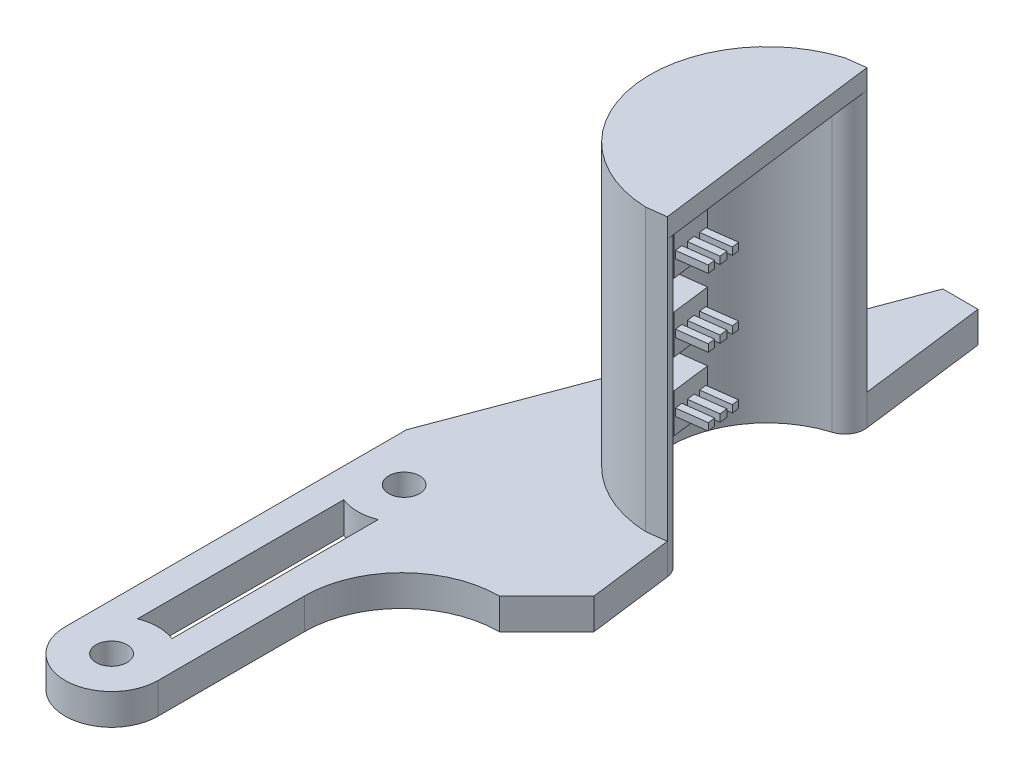
SolidWorks part; units mm, degrees
material "1060-H14"
ref_plane "Alzado" through (0, 0, 0) normal (0, 0, 1) x (1, 0, 0)
ref_plane "Planta" through (0, 0, 0) normal (0, 1, 0) x (1, 0, 0)
ref_plane "Vista lateral" through (0, 0, 0) normal (1, 0, 0) x (0, 0, -1)
sketch "Croquis1" plane through (0, 0, 0) normal (0, 1, 0) x (1, 0, 0)
  line L0 (-12.5, 40) -> (12.5, -40) construction
  line L1 (-12.5, 40) -> (12.5, 40) construction
  line L2 (-12.5, 40) -> (-12.5, -40) construction
  line L3 (-12.5, -40) -> (12.5, -40) construction
  line L4 (12.5, 40) -> (12.5, -40) construction
  line L5 (-12.5, 0) -> (-12.5, -40)
  line L6 (-12.5, -40) -> (-2.975, -40)
  line L7 (-2.975, -40) -> (-2.975, -20)
  line L8 (7.025, -10) -> (12.5, -10)
  line L9 (12.5, -10) -> (12.5, 40)
  line L10 (12.5, 40) -> (2.5, 40)
  line L11 (2.5, 40) -> (-12.5, 0)
  circle A0 centre (-7.7375, -5) radius 1.5875
  circle A1 centre (-7.7375, -35) radius 1.5875
  arc A2 (-2.975, -20) -> (7.025, -10) centre (7.025, -20) cw
  dimension "D5" = 3.175
  dimension "D6" = 3.175
  dimension "D12" = 10
  dimension "D1" = 25
  dimension "D2" = 80
  dimension "D3" = 9.525
  dimension "D4" = 30
  dimension "D7" = 4.7625
  dimension "D8" = 5
  dimension "D9" = 10
  dimension "D10" = 40
  dimension "D11" = 50
extrude "Saliente-Extruir1" add sketch "Croquis1" along normal blind 3.175
sketch "Croquis2" plane through (0, 3.175, 0) normal (0, 1, 0) x (1, 0, 0)
  line L0 (12.5, -10) -> (6.1, 40)
  line L1 (12.5, 40) -> (2.5, 40) construction
  line L2 (6.1, 40) -> (12.5, 40)
  line L3 (12.5, 40) -> (12.5, -10)
  dimension "D1" = 6.4
extrude "Cortar-Extruir1" cut sketch "Croquis2" against normal blind 3.175
sketch "Croquis3" plane through (0, 3.175, 0) normal (0, 1, 0) x (1, 0, 0)
  line L1 (-2.975, -40) -> (-2.975, -20) construction
  line L2 (-12.5, -35) -> (-12.5, -40)
  line L3 (-12.5, -40) -> (-2.975, -40)
  line L4 (-2.975, -40) -> (-2.975, -35)
  line L5 (-9.5, -9.4271) -> (-9.5, -30.5756)
  line L6 (-5.975, -14.8038) -> (-5.975, -30.5756)
  line L7 (-12.5, 0) -> (-12.5, -40) construction
  line L8 (-5.975, -14.8038) -> (-5.975, -9.4271)
  line L22 (7.025, -6) -> (7.9554, -6)
  line L23 (7.9554, -6) -> (3.2646, 30.6468)
  line L24 (3.2646, 30.6468) -> (-8.5, -0.7253)
  line L25 (-8.5, -0.7253) -> (-8.5, -36)
  line L26 (-8.5, -36) -> (-6.975, -36)
  line L27 (-6.975, -36) -> (-6.975, -20)
  line L28 (7.025, -6) -> (7.9554, -6)
  arc A2 (-9.5, -9.4271) -> (-5.975, -9.4271) centre (-7.7375, -5) ccw
  arc A3 (-12.5, -35) -> (-2.975, -35) centre (-7.7375, -35) ccw
  arc A4 (-5.975, -30.5756) -> (-9.5, -30.5756) centre (-7.7375, -35) ccw
  arc A6 (7.025, -6) -> (-6.975, -20) centre (7.025, -20) ccw
  dimension "D1" = 9.53
  dimension "D2" = 3
  dimension "D3" = 3
  dimension "D5" = 4
extrude "Cortar-Extruir3" cut sketch "Croquis3" against normal blind 10 contours A4 L6 L8 A2 L5 | A3 L4 L3 L2
sketch "Croquis4" plane through (0, 3.175, 0) normal (0, 1, 0) x (1, 0, 0)
  line L0 (6.1, 40) -> (12.5, -10) construction
  line L1 (7.025, -10) -> (11.8787, -5.1463)
  line L2 (11.8787, -5.1463) -> (12.5, -10)
  line L3 (12.5, -10) -> (7.025, -10)
  circle A0 centre (9.2741, 15.2023) radius 10
  dimension "D1" = 20
  dimension "D2" = 25
  dimension "D3" = 45
extrude "Cortar-Extruir4" cut sketch "Croquis4" against normal blind 10
fillet "Redondeo1" radius 2 2 edges at (8.0045, 1.5875, -25.1214) (10.5437, 1.5875, -5.2832)
sketch "Sketch1" plane through (0, 3.175, 0) normal (0, 1, 0) x (1, 0, 0)
  line L0 (5.788, 26.6848) -> (7.7718, 26.9387)
  line L1 (8.7925, 3.212) -> (10.7764, 3.4659)
  arc A0 (6.369, 24.771) -> (8.8728, 5.2104) centre (9.2741, 15.2023) ccw construction
  arc A1 (6.369, 24.771) -> (8.8728, 5.2104) centre (9.2741, 15.2023) ccw
  arc A2 (6.369, 24.771) -> (7.7718, 26.9387) centre (5.788, 26.6848) ccw construction
  arc A3 (6.369, 24.771) -> (7.7718, 26.9387) centre (5.788, 26.6848) ccw
  arc A4 (10.7764, 3.4659) -> (8.8728, 5.2104) centre (8.7925, 3.212) ccw construction
  arc A5 (10.7764, 3.4659) -> (8.8728, 5.2104) centre (8.7925, 3.212) ccw
  arc A6 (5.788, 26.6848) -> (5.788, 26.6848) centre (5.788, 26.6848) cw
  arc A7 (5.788, 26.6848) -> (8.7925, 3.212) centre (9.2741, 15.2023) ccw
  arc A8 (8.7925, 3.212) -> (8.7925, 3.212) centre (8.7925, 3.212) cw
  dimension "D1" = 2
extrude "Boss-Extrude1" add sketch "Sketch1" along normal blind 26.82
sketch "Sketch2" plane through (0, 29.995, 0) normal (0, 1, 0) x (1, 0, 0)
  line L0 (10.7764, 3.4659) -> (7.7718, 26.9387)
  line L2 (7.7718, 26.9387) -> (5.788, 26.6848)
  line L3 (8.7925, 3.212) -> (10.7764, 3.4659)
  line L4 (7.7718, 26.9387) -> (5.788, 26.6848)
  line L5 (8.7925, 3.212) -> (10.7764, 3.4659)
  arc A4 (5.788, 26.6848) -> (8.7925, 3.212) centre (9.2741, 15.2023) ccw
  arc A5 (10.7764, 3.4659) -> (8.8728, 5.2104) centre (8.7925, 3.212) ccw
  arc A6 (6.369, 24.771) -> (8.8728, 5.2104) centre (9.2741, 15.2023) ccw
  arc A7 (6.369, 24.771) -> (7.7718, 26.9387) centre (5.788, 26.6848) ccw
  arc A8 (5.788, 26.6848) -> (8.7925, 3.212) centre (9.2741, 15.2023) ccw
  dimension "D1" = 0
extrude "Boss-Extrude2" add sketch "Sketch2" along normal blind 2
sketch "Sketch4" plane through (0, 0, 0) normal (0, -1, 0) x (1, 0, 0)
  line L1 (1.2911, -69.7572) -> (-1.3089, -69.7572)
  line L2 (-1.3089, -69.7572) -> (2.5, -40)
  line L3 (6.1, -40) -> (7.7718, -26.9387) construction
  line L4 (6.1, -40) -> (2.5, -40) construction
  line L5 (5.1, -40) -> (2.5, -40)
  line L6 (5.1, -40) -> (1.2911, -69.7572)
  dimension "D1" = 30
  dimension "D2" = 1
extrude "Boss-Extrude3" [suppressed] add sketch "Sketch4" against normal up to surface (31.995 mm away)
sketch "Sketch5" [suppressed] plane through (10.0553, 0, -1.2871) normal (0.9919, 0, -0.127) x (-0.127, 0, -0.9919)
  line L2 (39.0288, 31.995) -> (39.0288, 3.175) construction
  line L3 (69.0288, 31.995) -> (39.0288, 31.995) construction
  circle A0 centre (41.5288, 29.495) radius 1.59
  circle A1 centre (46.5288, 29.495) radius 1.59
  circle A2 centre (51.5288, 29.495) radius 1.59
  circle A3 centre (56.5288, 29.495) radius 1.59
  circle A4 centre (61.5288, 29.495) radius 1.59
  circle A5 centre (66.5288, 29.495) radius 1.59
  circle A6 centre (46.5288, 24.995) radius 1.59
  circle A7 centre (51.5288, 24.995) radius 1.59
  circle A8 centre (56.5288, 24.995) radius 1.59
  circle A9 centre (61.5288, 24.995) radius 1.59
  circle A10 centre (66.5288, 24.995) radius 1.59
  circle A11 centre (46.5288, 20.495) radius 1.59
  circle A12 centre (51.5288, 20.495) radius 1.59
  circle A13 centre (56.5288, 20.495) radius 1.59
  circle A14 centre (61.5288, 20.495) radius 1.59
  circle A15 centre (66.5288, 20.495) radius 1.59
  circle A16 centre (46.5288, 15.995) radius 1.59
  circle A17 centre (51.5288, 15.995) radius 1.59
  circle A18 centre (56.5288, 15.995) radius 1.59
  circle A19 centre (61.5288, 15.995) radius 1.59
  circle A20 centre (66.5288, 15.995) radius 1.59
  circle A21 centre (46.5288, 11.495) radius 1.59
  circle A22 centre (51.5288, 11.495) radius 1.59
  circle A23 centre (56.5288, 11.495) radius 1.59
  circle A24 centre (61.5288, 11.495) radius 1.59
  circle A25 centre (66.5288, 11.495) radius 1.59
  circle A26 centre (46.5288, 6.995) radius 1.59
  circle A27 centre (51.5288, 6.995) radius 1.59
  circle A28 centre (56.5288, 6.995) radius 1.59
  circle A29 centre (61.5288, 6.995) radius 1.59
  circle A30 centre (66.5288, 6.995) radius 1.59
  circle A31 centre (46.5288, 2.495) radius 1.59
  circle A32 centre (51.5288, 2.495) radius 1.59
  circle A33 centre (56.5288, 2.495) radius 1.59
  circle A34 centre (61.5288, 2.495) radius 1.59
  circle A35 centre (66.5288, 2.495) radius 1.59
  circle A36 centre (41.5288, 24.995) radius 1.59
  circle A37 centre (41.5288, 20.495) radius 1.59
  circle A38 centre (41.5288, 15.995) radius 1.59
  circle A39 centre (41.5288, 11.495) radius 1.59
  circle A40 centre (41.5288, 6.995) radius 1.59
  circle A41 centre (41.5288, 2.495) radius 1.59
  dimension "D1" = 3.18
  dimension "D2" = 2.5
  dimension "D3" = 2.5
  dimension "D4" = 6
  dimension "D5" = 7
extrude "Boss-Extrude4" [suppressed] add sketch "Sketch5" along normal blind 1
ref_plane "Plane1" through (4.0958, 0, -0.5243) normal (0.9919, 0, -0.127) x (-0.127, 0, -0.9919)
sketch "Sketch6" plane through (4.0958, 0, -0.5243) normal (0.9919, 0, -0.127) x (-0.127, 0, -0.9919)
  line L0 (4.0417, 0) -> (23.7619, 0) construction
  line L1 (15.9018, 28.995) -> (11.9018, 28.995)
  line L2 (15.9018, 28.995) -> (15.9018, 24.995)
  line L3 (15.9018, 24.995) -> (11.9018, 24.995)
  line L4 (11.9018, 28.995) -> (11.9018, 24.995)
  line L5 (15.9018, 28.995) -> (11.9018, 24.995) construction
  line L6 (15.9018, 24.995) -> (11.9018, 28.995) construction
  line L7 (2.0697, 29.995) -> (25.734, 29.995) construction
  point P0 (13.9018, 26.995)
  point P8 (13.9018, 0)
  dimension "D1" = 4
  dimension "D2" = 4
  dimension "D3" = 1
extrude "Boss-Extrude5" add sketch "Sketch6" against normal up to surface (2.798 mm away)
sketch "Sketch7" plane through (4.0958, 0, -0.5243) normal (0.9919, 0, -0.127) x (-0.127, 0, -0.9919)
  line L1 (15.7043, 27.37) -> (14.9543, 27.37)
  line L2 (15.7043, 27.37) -> (15.7043, 26.62)
  line L3 (15.7043, 26.62) -> (14.9543, 26.62)
  line L4 (14.9543, 27.37) -> (14.9543, 26.62)
  line L5 (15.7043, 27.37) -> (14.9543, 26.62) construction
  line L6 (15.7043, 26.62) -> (14.9543, 27.37) construction
  line L7 (14.3043, 27.37) -> (13.4994, 27.37)
  line L8 (14.3043, 27.37) -> (14.3043, 26.62)
  line L9 (14.3043, 26.62) -> (13.4994, 26.62)
  line L10 (13.4994, 27.37) -> (13.4994, 26.62)
  line L11 (14.3043, 27.37) -> (13.4994, 26.62) construction
  line L12 (14.3043, 26.62) -> (13.4994, 27.37) construction
  line L13 (12.8494, 27.37) -> (12.0994, 27.37)
  line L14 (12.8494, 27.37) -> (12.8494, 26.62)
  line L15 (12.8494, 26.62) -> (12.0994, 26.62)
  line L16 (12.0994, 27.37) -> (12.0994, 26.62)
  line L17 (12.8494, 27.37) -> (12.0994, 26.62) construction
  line L18 (12.8494, 26.62) -> (12.0994, 27.37) construction
  line L19 (11.9018, 24.995) -> (15.9018, 24.995) construction
  line L20 (15.9018, 24.995) -> (15.9018, 28.995) construction
  point P0 (15.3293, 26.995)
  point P5 (13.9018, 26.995)
  point P10 (12.4744, 26.995)
  point P20 (13.9018, 24.995)
  point P22 (15.9018, 26.995)
  dimension "D1" = 0.75
  dimension "D2" = 0.75
  dimension "D3" = 0.65
  dimension "D4" = 0.65
extrude "Boss-Extrude6" add sketch "Sketch7" along normal blind 3
pattern_linear "LPattern1" count 4 spacing 7 along (0, -1, 0) of "Boss-Extrude5", "Boss-Extrude6"
